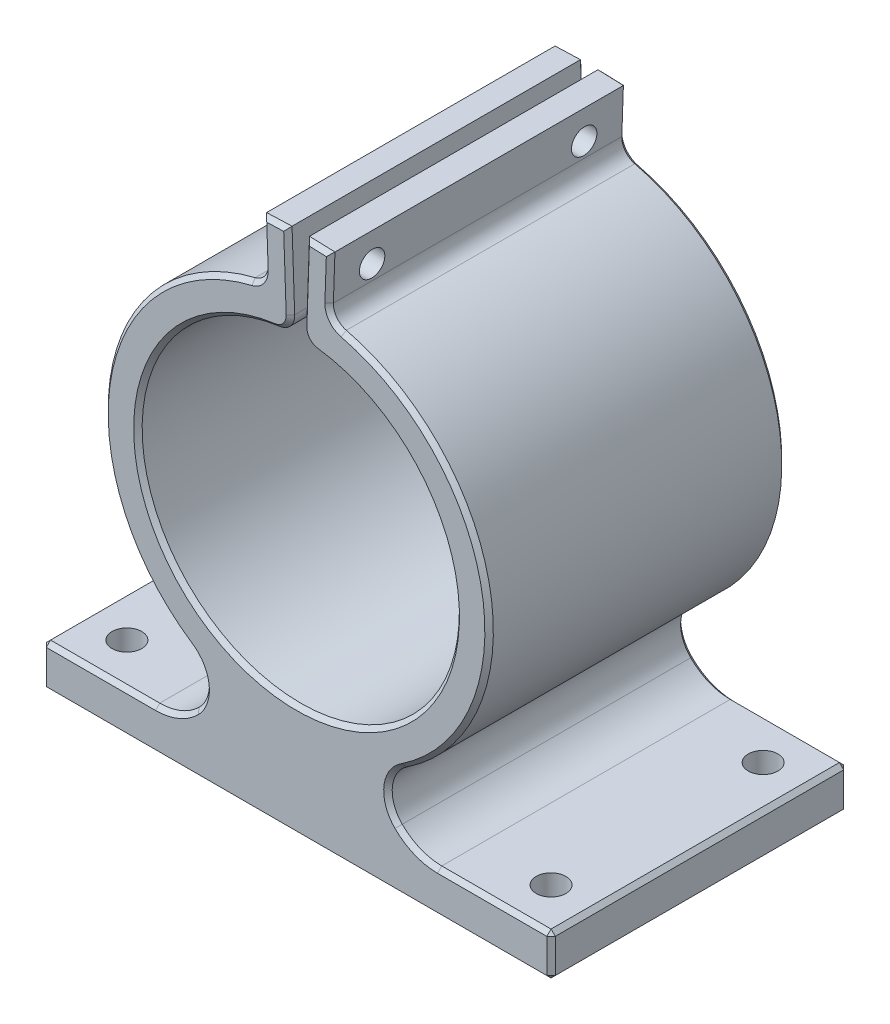
SolidWorks part; units mm, degrees
ref_plane "Front Plane" through (0, 0, 0) normal (0, 0, 1) x (1, 0, 0)
ref_plane "Top Plane" through (0, 0, 0) normal (0, 1, 0) x (1, 0, 0)
ref_plane "Right Plane" through (0, 0, 0) normal (1, 0, 0) x (0, 0, -1)
sketch "Sketch1" plane through (0, 0, 0) normal (0, 0, 1) x (1, 0, 0)
  line L0 (0, 0) -> (0, -32)
  line L1 (-30, -32) -> (30, -32)
  line L2 (30, -32) -> (30, -27)
  line L3 (0, 0) -> (0.7922, 22.6862)
  line L4 (30, -27) -> (16.6213, -27)
  line L5 (10, -20.3787) -> (10, -15.8016)
  line L6 (-30, -32) -> (-30, -27)
  line L7 (-30, -27) -> (-16.6213, -27)
  line L8 (-10, -20.3787) -> (-10, -15.8016)
  line L9 (0, 0) -> (-0.7922, 22.6862)
  line L10 (0.7922, 22.6862) -> (1.0296, 29.4829)
  line L11 (1.0296, 29.4829) -> (4.0277, 29.3782)
  line L12 (4.0277, 29.3782) -> (3.7834, 22.3825)
  line L13 (-0.7922, 22.6862) -> (-1.0296, 29.4829)
  line L14 (-1.0296, 29.4829) -> (-4.0277, 29.3782)
  line L15 (-4.0277, 29.3782) -> (-3.7834, 22.3825)
  arc A0 (-0.6526, 18.6886) -> (0.6526, 18.6886) centre (0, 0) ccw
  arc A1 (-0.7922, 22.6862) -> (0.7922, 22.6862) centre (0, 0) ccw
  arc A2 (16.6213, -27) -> (10, -20.3787) centre (16.6213, -20.3787) cw
  arc A3 (-16.6213, -27) -> (-10, -20.3787) centre (-16.6213, -20.3787) ccw
  dimension "D1" = 37.4
  dimension "D2" = 4
  dimension "D4" = 32
  dimension "D3" = 178
  dimension "D5" = 5
  dimension "D6" = 30
  dimension "D7" = 10
  dimension "D8" = 3
  dimension "D9" = 7
extrude "Boss-Extrude1" add sketch "Sketch1" along normal blind 35 contours L9 A1 L8 A0 | L8 A1 L0 A0 | L0 A1 L5 A0 | L5 A1 L3 A0 | L4 A2 A1 L0 L1 L2 | A3 L7 L6 L1 L0 A1 | A1 L13 L14 L15 | A1 L12 L11 L10
sketch "Sketch2" plane through (0, 0, 0) normal (1, 0, 0) x (0, 0, -1)
  line L0 (-35, 29.3782) -> (-35, 22.3825) construction
  line L1 (-35, 29.3782) -> (-35, 22.3825)
  line L2 (-35, 25.8804) -> (0, 25.8804) construction
  line L3 (0, 29.3782) -> (0, 22.3825) construction
  circle A0 centre (-30, 25.8804) radius 1.5
  circle A1 centre (-5, 25.8804) radius 1.5
  dimension "D1" = 3
  dimension "D2" = 5
  dimension "D3" = 5
extrude "Cut-Extrude1" cut sketch "Sketch2" against normal through all both and the other way through all contours L2 A1 | L2 A0 | A0 L2 | A1 L2
sketch "Sketch3" plane through (0, -27, 0) normal (0, 1, 0) x (1, 0, 0)
  line L8 (25, -5) -> (-25, -5)
  line L9 (25, -30) -> (25, -5)
  line L10 (-25, -30) -> (25, -30)
  line L11 (-25, -5) -> (-25, -30)
  line L12 (25, -5) -> (-25, -5) construction
  line L13 (25, -30) -> (25, -5) construction
  line L14 (-25, -30) -> (25, -30) construction
  line L15 (-25, -5) -> (-25, -30) construction
  circle A0 centre (-25, -5) radius 1.75
  circle A1 centre (-25, -30) radius 1.75
  circle A2 centre (25, -30) radius 1.75
  circle A3 centre (25, -5) radius 1.75
  dimension "D2" = 3.5
  dimension "D1" = 5
extrude "Cut-Extrude2" cut sketch "Sketch3" against normal through all
fillet "Fillet1" radius 4 2 edges at (-10, -20.3787, 17.5) (10, -20.3787, 17.5)
fillet "Fillet2" radius 2 4 edges at (3.7834, 22.3825, 17.5) (-0.6526, 18.6886, 17.5) (0.6526, 18.6886, 17.5) (-3.7834, 22.3825, 17.5)
chamfer "Chamfer1" distance 0.5 angle 45 48 edges at (30, -29.5, 0) (30, -29.5, 35) (23.3107, -27, 0) (23.3107, -27, 35) (14.0993, -26.5009, 0) (14.0993, -26.5009, 35) (-22.3579, 3.9261, 35) (-22.3579, 3.9261, 0) (22.3579, 3.9261, 0) (22.3579, 3.9261, 35) (3.935, 26.7237, 35) (3.935, 26.7237, 0) (2.5287, 29.4306, 0) (2.5287, 29.4306, 35) (0.8743, 25.0368, 0) (0.8743, 25.0368, 35) (0, -18.7, 0) (0, -18.7, 35) (-0.8743, 25.0368, 35) (-0.8743, 25.0368, 0) (-2.5287, 29.4306, 0) (-2.5287, 29.4306, 35) (-3.935, 26.7237, 0) (-3.935, 26.7237, 35) (-14.0993, -26.5009, 35) (-14.0993, -26.5009, 0) (-23.3107, -27, 0) (-23.3107, -27, 35) (-30, -29.5, 0) (-30, -29.5, 35) (0, -32, 0) (0, -32, 35) (-4.2472, 22.7913, 35) (-4.2472, 22.7913, 0) (-10.794, -21.8498, 35) (-10.794, -21.8498, 0) (10.794, -21.8498, 35) (10.794, -21.8498, 0) (4.2472, 22.7913, 35) (4.2472, 22.7913, 0) (1.1909, 19.2291, 35) (1.1909, 19.2291, 0) (-1.1909, 19.2291, 35) (-1.1909, 19.2291, 0) (-30, -27, 17.5) (-30, -32, 17.5) (30, -32, 17.5) (30, -27, 17.5)
